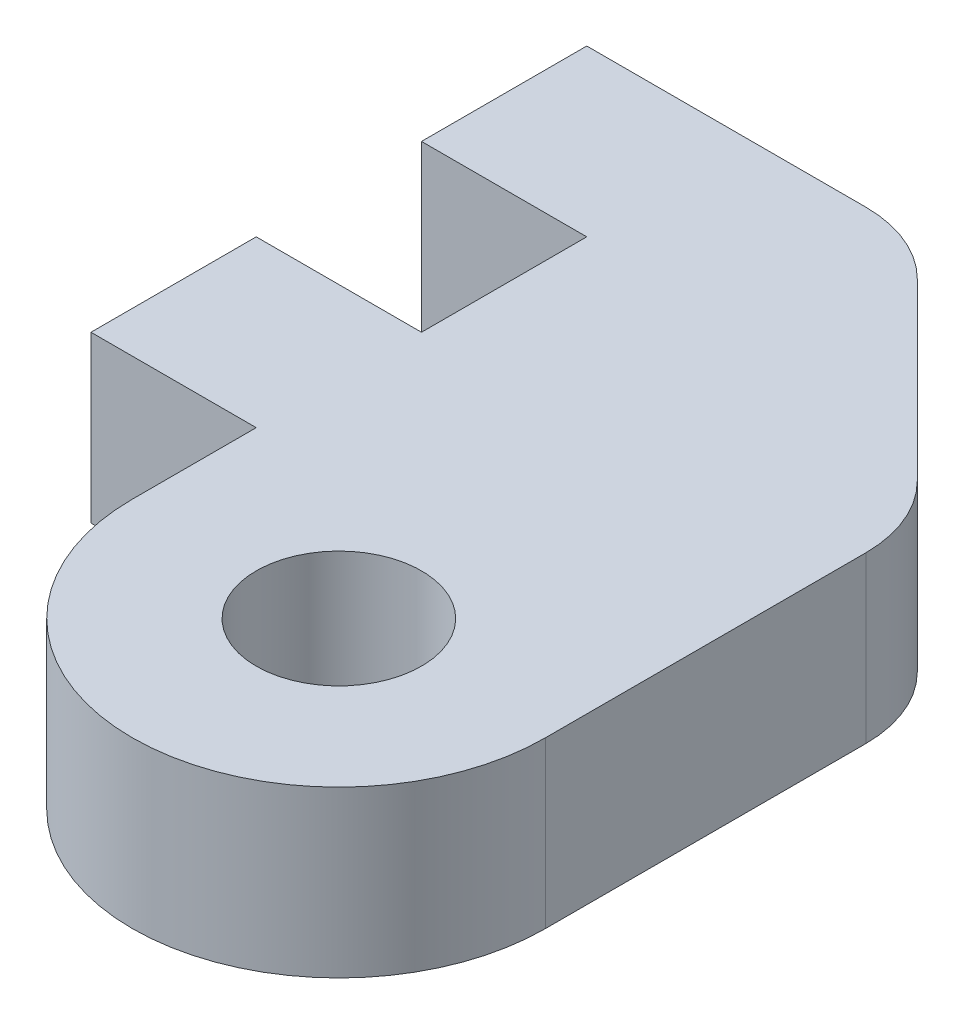
SolidWorks part; units mm, degrees
ref_plane "Front Plane" through (0, 0, 0) normal (0, 0, 1) x (1, 0, 0)
ref_plane "Top Plane" through (0, 0, 0) normal (0, 1, 0) x (1, 0, 0)
ref_plane "Right Plane" through (0, 0, 0) normal (1, 0, 0) x (0, 0, -1)
sketch "Sketch1" plane through (0, 0, 0) normal (0, 1, 0) x (1, 0, 0)
  line L5 (5, 0) -> (-5, 0)
  line L6 (5, 0) -> (5, 15)
  line L7 (5, 15) -> (-5, 15)
  line L8 (-5, 0) -> (-5, 15)
  line L9 (-5, 15) -> (-9, 15)
  line L10 (-5, 15) -> (-5, 11)
  line L11 (-5, 11) -> (-9, 11)
  line L12 (-9, 15) -> (-9, 11)
  line L13 (-5, 7) -> (-9, 7)
  line L14 (-5, 7) -> (-5, 3)
  line L15 (-5, 3) -> (-9, 3)
  line L16 (-9, 7) -> (-9, 3)
  circle A0 centre (0, 0) radius 2
  circle A1 centre (0, 0) radius 5
  dimension "D1" = 4
  dimension "D2" = 10
  dimension "D3" = 15
  dimension "D4" = 4
  dimension "D5" = 4
  dimension "D6" = 4
  dimension "D7" = 4
extrude "Boss-Extrude1" add sketch "Sketch1" along normal blind 4 contours L9 L12 L11 L8 | L13 L16 L15 L8 | A1 L6 L7 L8 | L5 A1 A0 | L5 A1 A0
chamfer "Chamfer1" distance 6 angle 45 1 edges at (5, 2, -15)
fillet "Fillet1" radius 3 2 edges at (5, 2, -9) (-1, 2, -15)
equation "\"D6@Sketch1\"=\"D5@Sketch1\""
